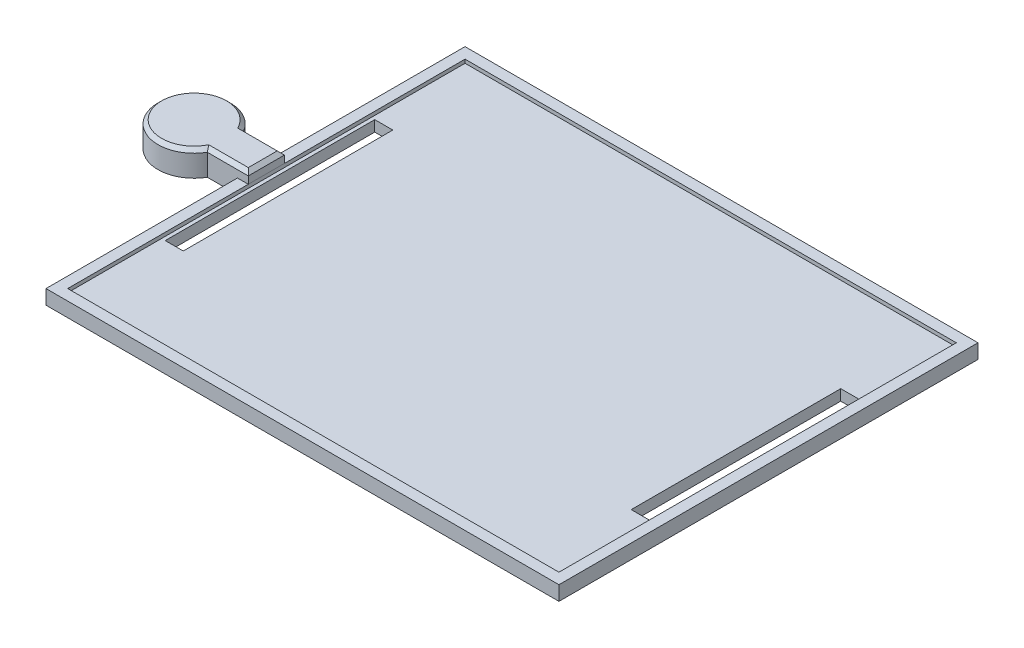
SolidWorks part; units mm, degrees
ref_plane "Front Plane" through (0, 0, 0) normal (0, 0, 1) x (1, 0, 0)
ref_plane "Top Plane" through (0, 0, 0) normal (0, 1, 0) x (1, 0, 0)
ref_plane "Right Plane" through (0, 0, 0) normal (1, 0, 0) x (0, 0, -1)
sketch "Sketch2" plane through (0, 0, 0) normal (0, 1, 0) x (1, 0, 0)
  line L1 (-71, -58) -> (71, -58)
  line L2 (-71, -58) -> (-71, 58)
  line L3 (-71, 58) -> (71, 58)
  line L4 (71, -58) -> (71, 58)
  line L5 (-71, -58) -> (71, 58) construction
  line L6 (-71, 58) -> (71, -58) construction
  point P0 (0, 0)
  dimension "D1" = 142
  dimension "D2" = 116
extrude "Boss-Extrude2" add sketch "Sketch2" along normal blind 4
shell "Shell1" thickness 3
sketch "Sketch4" plane through (0, 0, 0) normal (0, -1, 0) x (1, 0, 0)
  line L1 (-41, 15) -> (-31, 15)
  line L2 (-41, 15) -> (-41, -15)
  line L3 (-41, -15) -> (-31, -15)
  line L4 (-31, 15) -> (-31, -15)
  line L5 (-41, 15) -> (-31, -15) construction
  line L6 (-41, -15) -> (-31, 15) construction
  line L7 (18.7, 0) -> (-18.7, 0) construction
  line L10 (24.05, 15) -> (14.05, -15) construction
  line L11 (24.05, -15) -> (14.05, 15) construction
  line L12 (24.05, -15) -> (14.05, -15)
  line L13 (24.05, 15) -> (14.05, 15)
  line L14 (24.05, 15) -> (24.05, -15)
  line L15 (14.05, 15) -> (14.05, -15)
  line L16 (-5.95, 15) -> (-15.95, -15) construction
  line L17 (-5.95, -15) -> (-15.95, 15) construction
  line L18 (-5.95, -15) -> (-15.95, -15)
  line L19 (-5.95, 15) -> (-15.95, 15)
  line L20 (-5.95, 15) -> (-5.95, -15)
  line L21 (-15.95, 15) -> (-15.95, -15)
  line L22 (-71, -58) -> (-71, 58) construction
  point P0 (-36, 0)
  point P9 (19.05, 0)
  point P19 (-10.95, 0)
  dimension "D2" = 30
  dimension "D3" = 10
  dimension "D4" = 30
  dimension "D5" = 10
  dimension "D6" = 10
  dimension "D7" = 20
  dimension "D11" = 65.05
  dimension "D12" = 30
  dimension "D13" = 30
extrude "Boss-Extrude4" add sketch "Sketch4" along normal blind 30
sketch "Sketch5" plane through (-41, 0, 0) normal (-1, 0, 0) x (0, 0, 1)
  line L1 (-15, -30) -> (-15, 0) construction
  line L2 (15, -30) -> (-15, -30) construction
  line L3 (-15, -15) -> (-15, -30)
  line L4 (-15, -30) -> (15, -30)
  line L5 (15, -30) -> (15, -15)
  line L6 (15, -15) -> (15, -30)
  line L10 (15, 0) -> (-15, 0)
  line L11 (15, 0) -> (-15, 0)
  line L12 (-15, -30) -> (15, -30)
  line L13 (-15, -30) -> (15, -30)
  line L14 (15, -30) -> (15, 0)
  line L20 (-15, 0) -> (-15, -30)
  line L21 (15, -30) -> (15, 0)
  line L27 (-15, 0) -> (-15, -30)
  arc A0 (-15, -15) -> (15, -15) centre (0, -15) ccw
  line M2 (-15, 0) -> (-15, -30)
  line M3 (-15, -30) -> (15, -30)
  line M4 (15, -30) -> (15, 0)
  dimension "D1" = 0
extrude "Cut-Extrude1" cut sketch "Sketch5" against normal through all both and the other way through all contours A0 M2 M3 | A0 L4 M4
sketch "Sketch6" plane through (-41, 0, 0) normal (-1, 0, 0) x (0, 0, 1)
  line L0 (0, -18.7) -> (0, 18.7) construction
  line L1 (0, 0) -> (3, 0)
  line L2 (0, 0) -> (0, -3.5)
  line L3 (0, -3.5) -> (3, -3.5)
  line L4 (3, 0) -> (3, -3.5)
  dimension "D1" = 3
  dimension "D2" = 3.5
extrude "Cut-Extrude2" cut sketch "Sketch6" against normal through all both and the other way through all
fillet "Fillet2" radius 2 12 edges at (-5.95, 0, -7.5) (-5.95, 0, 9) (24.05, 0, -7.5) (24.05, 0, 9) (14.05, 0, -7.5) (14.05, 0, 9) (-15.95, 0, 9) (-15.95, 0, -7.5) (-31, 0, -7.5) (-31, 0, 9) (-41, 0, 9) (-41, 0, -7.5)
ref_plane "Plane1" through (-41, -15, -15) normal (0, 1, 0) x (1, 0, 0)
sketch "Sketch9" plane through (-41, 0, 0) normal (-1, 0, 0) x (0, 0, 1)
  line L1 (-11.25, -21.05) -> (11.25, -21.05)
  line L2 (-11.25, -21.05) -> (-11.25, -8.95)
  line L3 (-11.25, -8.95) -> (11.25, -8.95)
  line L4 (11.25, -21.05) -> (11.25, -8.95)
  line L5 (-11.25, -21.05) -> (11.25, -8.95) construction
  line L6 (-11.25, -8.95) -> (11.25, -21.05) construction
  point P0 (0, -15)
  point P5 (0, -15)
  dimension "D1" = 12.1
  dimension "D2" = 22.5
extrude "Cut-Extrude3" cut sketch "Sketch9" against normal up to surface (10 mm away) and the other way through all up to face at (-31, -7.5, 0.75)
sketch "Sketch10" plane through (14.05, 0, 0) normal (-1, 0, 0) x (0, 0, 1)
  line L1 (0, -18.7) -> (0, 18.7) construction
  circle A0 centre (0, -20) radius 4
  arc A1 (-15, -15) -> (15, -15) centre (0, -15) ccw construction
  point P7 (0, -30)
  dimension "D3" = 8
  dimension "D2" = 10
sketch "Sketch11" plane through (-5.95, 0, 0) normal (1, 0, 0) x (0, 0, -1)
  arc A2 (-15, -15) -> (15, -15) centre (0, -15) ccw construction
  circle A3 centre (0, -20) radius 4.25
  circle A5 centre (0, -20) radius 5.5
  point P5 (0, -30)
  dimension "D1" = 10
  dimension "D2" = 8.5
  dimension "D3" = 11
extrude "Boss-Extrude6" add sketch "Sketch11" along normal blind 17.5
ref_plane "Plane2" through (0, -15.75, 0) normal (0, -1, 0) x (-1, 0, 0)
sketch "Sketch13" plane through (-41, 0, 0) normal (-1, 0, 0) x (0, 0, 1)
  line L0 (11.25, -8.95) -> (11.25, -21.05) construction
  line L1 (11.25, -8.95) -> (11.25, -21.05)
  point P0 (13.85, -15)
  point P4 (11.25, -15)
  dimension "D1" = 2.6
sketch "Sketch17" plane through (-41, 0, 0) normal (-1, 0, 0) x (0, 0, 1)
  point P0 (13.85, -15)
hole_wizard "M3x0.5 Tapped Hole1" positions "Sketch17" profile "Sketch18" tap size "M3x0.5" standard "ANSI Metric"
sketch "Sketch18" plane through (-41, -15, 13.85) normal (0, 1, 0) x (0, 0, 1)
  line L0 (0, 0) -> (0, 10.6609)
  line L1 (0, 10.6609) -> (1.1, 10)
  line L2 (1.1, 10) -> (1.1, 0)
  line L5 (1.1, 0) -> (0, 0)
  line L10 (0, 10.6609) -> (-1.1, 10) construction
  line L11 (0, -6.35) -> (0, 107.95) construction
  dimension "Tap Drill Dia." = 2.2
  dimension "Tap Drill Depth" = 10
  dimension "Drill Angle" = 118
cosmetic thread "Hole Thread1" parameters "D1"=2.5, "D2"=3
sketch "Sketch19" plane through (0, 4, 0) normal (0, 1, 0) x (1, 0, 0)
  line L0 (-68, 55) -> (-68, -55) construction
  line L1 (-68, 5) -> (-88, 5)
  line L2 (-68, 5) -> (-68, -5)
  line L3 (-68, -5) -> (-88, -5)
  line L4 (-88, 5) -> (-88, -5)
  line L5 (-68, 55) -> (-68, -55)
  line L6 (-18.7, 0) -> (18.7, 0) construction
  circle A1 centre (-88, 0) radius 10
  line M7 (-71, 58) -> (-71, -58)
  line M11 (-68, -55) -> (-68, 55)
  dimension "D4" = 20
  dimension "D1" = 10
  dimension "D2" = 5
  dimension "D3" = 20
extrude "Boss-Extrude7" add sketch "Sketch19" along normal blind 3 and the other way blind 4 separate body contours L1 A1 L3 L4 | L3 A1 L1 L4 | A1 L3 L1 M7 | L3 L1 M11 M7
chamfer "Chamfer1" distance 1 angle 45 4 edges at (-73.6699, 7, 5) (-98, 7, 0) (-68, 7, 0) (-73.6699, 7, -5)
sketch "Sketch27" plane through (0, 0, 0) normal (0, -1, 0) x (1, 0, 0)
  line L2 (-43, 20) -> (-29, 20)
  line L3 (-43, 20) -> (-43, -15)
  line L4 (71, 58) -> (-71, 58)
  line L5 (-71, 58) -> (-71, -58)
  line L6 (-71, -58) -> (71, -58)
  line L7 (71, -58) -> (71, 58)
  line L8 (71, 58) -> (-71, 58)
  line L9 (-71, 58) -> (-71, -58)
  line L10 (-71, -58) -> (71, -58)
  line L11 (71, -58) -> (71, 58)
  line L12 (-43, -15) -> (-29, -15)
  line L13 (-29, 20) -> (-29, -15)
  point P2 (0, 0)
  dimension "D2" = 14
  dimension "D3" = 35
  dimension "D1" = 0
extrude "Boss-Extrude10" add sketch "Sketch27" along normal blind 45 contours L12 L13 L2 L3
sketch "Sketch28" plane through (-43, 0, 0) normal (-1, 0, 0) x (0, 0, 1)
  line L0 (15, -30) -> (15, -15) construction
  line L1 (15, -15) -> (15, -30) construction
  line L2 (-15, -30) -> (15, -30) construction
  line L3 (-15, -15) -> (-15, -30) construction
  line L4 (15, 0) -> (-15, 0) construction
  line L5 (15, -30) -> (15, 0) construction
  line L6 (-15, -30) -> (15, -30) construction
  line L7 (-15, 0) -> (-15, -30) construction
  line L8 (15, -30) -> (15, -15)
  line L9 (15, -15) -> (15, -30)
  line L10 (-15, -30) -> (15, -30)
  line L11 (-15, -15) -> (-15, -30)
  line L12 (15, 0) -> (-15, 0)
  line L13 (15, -30) -> (15, 0)
  line L14 (-15, -30) -> (15, -30)
  line L15 (-15, 0) -> (-15, -30)
  line L16 (20, -45) -> (-15, -45) construction
  arc A0 (-15, -15) -> (15, -15) centre (0, -15) ccw construction
  arc A1 (-15, -15) -> (15, -15) centre (0, -15) ccw
  circle A2 centre (0, -30) radius 15
  line M1 (20, -45) -> (20, 0)
  line M3 (-15, 0) -> (-15, -45)
  line M4 (-15, -45) -> (20, -45)
extrude "Cut-Extrude4" cut sketch "Sketch28" against normal blind 45 contours A2 M4 M1 | A2 M3 M4
sketch "Sketch29" plane through (-43, 0, 0) normal (-1, 0, 0) x (0, 0, 1)
  line L1 (-11.375, -18.925) -> (11.375, -18.925)
  line L2 (-11.375, -18.925) -> (-11.375, -31.075)
  line L3 (-11.375, -31.075) -> (11.375, -31.075)
  line L4 (11.375, -18.925) -> (11.375, -31.075)
  arc A0 (-15, -30) -> (15, -30) centre (0, -30) ccw construction
  arc A1 (-15, -30) -> (15, -30) centre (0, -30) ccw
  point P4 (11.375, -25)
  point P8 (0, -45)
  point P9 (0, -31.075)
  dimension "D1" = 22.75
  dimension "D2" = 12.15
  dimension "D3" = 20
extrude "Cut-Extrude5" cut sketch "Sketch29" against normal up to next (14 mm away) contours L4 L1 L2 L3
sketch "Sketch30" plane through (-43, 0, 0) normal (-1, 0, 0) x (0, 0, 1)
  line L0 (11.375, -18.925) -> (11.375, -31.075) construction
  line L1 (11.375, -18.925) -> (11.375, -31.075)
  point P0 (13.875, -25)
  point P1 (11.375, -18.925)
  point P4 (11.375, -25)
  point P5 (13.875, -25)
  point P28 (13.1524, -20.1287)
  dimension "D1" = 2.5
hole_wizard "M2 Clearance Hole1" positions "Sketch30" profile "Sketch36" hole size "M2" standard "ISO"
sketch "Sketch36" plane through (-43, -25, 13.875) normal (0, 1, 0) x (0, 0, 1)
  line L0 (0, 0) -> (0, 14.721)
  line L1 (0, 14.721) -> (1.2, 14)
  line L2 (1.2, 14) -> (1.2, 0)
  line L5 (1.2, 0) -> (0, 0)
  line L10 (0, 14.721) -> (-1.2, 14) construction
  line L11 (0, -6.35) -> (0, 107.95) construction
  dimension "Hole Dia." = 2.4
  dimension "Hole Depth" = 14
  dimension "Drill Angle" = 118
sketch "Sketch37" plane through (14.05, 0, 0) normal (-1, 0, 0) x (0, 0, 1)
  circle A0 centre (0, -20) radius 4.25 construction
  circle A1 centre (0, -20) radius 4.25
extrude "Cut-Extrude6" cut sketch "Sketch37" against normal through all
sketch "Sketch38" plane through (0, 0, 0) normal (0, -1, 0) x (1, 0, 0)
  line L0 (-71, 58) -> (71, 58) construction
  line L1 (-67, 29) -> (-62, 29)
  line L2 (-67, 29) -> (-67, -29)
  line L3 (-67, -29) -> (-62, -29)
  line L4 (-62, 29) -> (-62, -29)
  line L5 (-71, -58) -> (-71, 58) construction
  line L6 (-71, -58) -> (71, -58)
  line L7 (71, -58) -> (0, -58)
  line L8 (0, -58) -> (0, 58)
  line L9 (67, -29) -> (62, -29)
  line L10 (62, 29) -> (62, -29)
  line L11 (67, 29) -> (62, 29)
  line L12 (67, 29) -> (67, -29)
  dimension "D1" = 29
  dimension "D2" = 4
  dimension "D3" = 5
  dimension "D4" = 58
extrude "Cut-Extrude7" cut sketch "Sketch38" against normal through all contours L4 L1 L2 L3 | L12 L11 L10 L9
